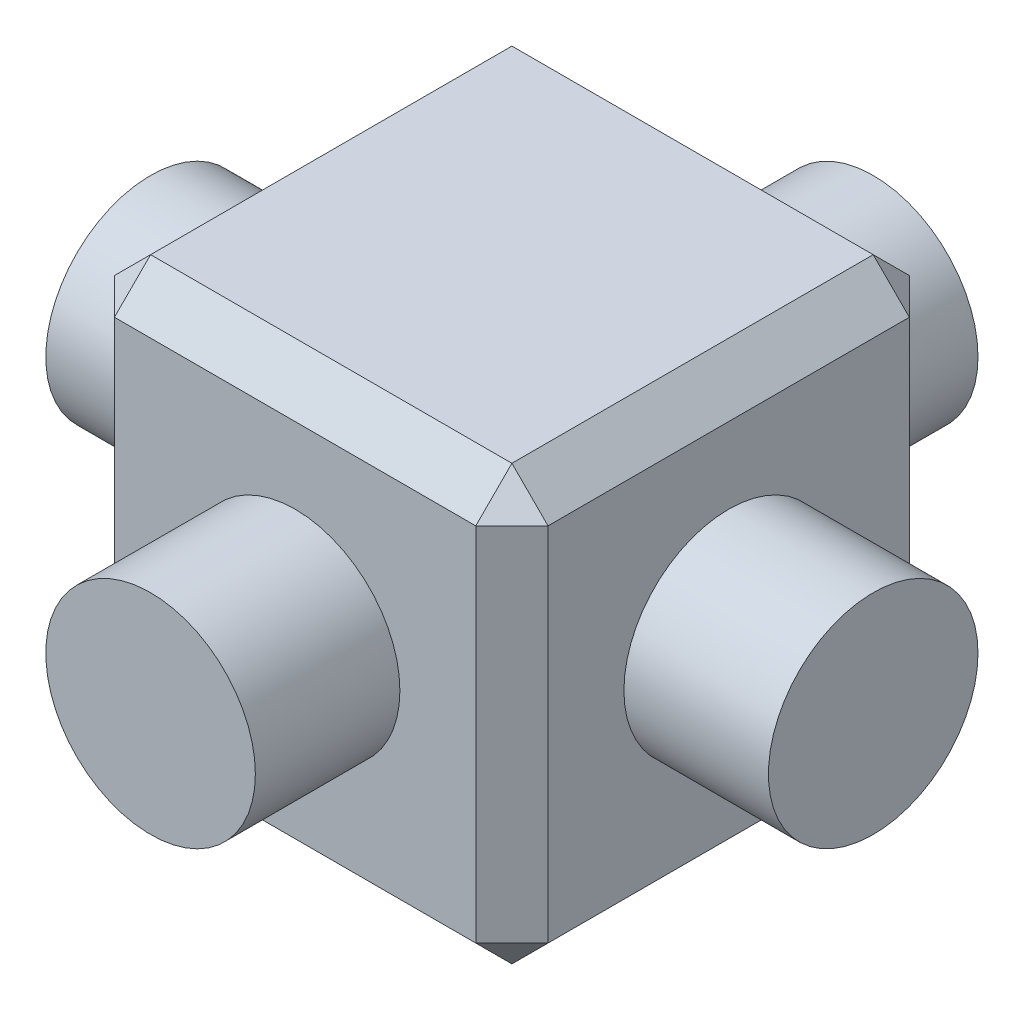
SolidWorks part; units mm, degrees
ref_plane "Front Plane" through (0, 0, 0) normal (0, 0, 1) x (1, 0, 0)
ref_plane "Top Plane" through (0, 0, 0) normal (0, 1, 0) x (1, 0, 0)
ref_plane "Right Plane" through (0, 0, 0) normal (1, 0, 0) x (0, 0, -1)
sketch "Sketch1" plane through (0, 0, 0) normal (0, 1, 0) x (1, 0, 0)
  line L1 (-3, -3) -> (3, -3)
  line L2 (-3, -3) -> (-3, 3)
  line L3 (-3, 3) -> (3, 3)
  line L4 (3, -3) -> (3, 3)
  line L5 (-3, -3) -> (3, 3) construction
  line L6 (-3, 3) -> (3, -3) construction
  point P0 (0, 0)
  dimension "D1" = 6
extrude "Boss-Extrude1" add sketch "Sketch1" along normal blind 6
sketch "Sketch2" plane through (3, 0, 0) normal (1, 0, 0) x (0, 0, -1)
  circle A0 centre (0, 3) radius 1.45
extrude "Boss-Extrude2" add sketch "Sketch2" along normal blind 2 and the other way blind 8
sketch "Sketch3" plane through (0, 0, 3) normal (0, 0, 1) x (1, 0, 0)
  circle A0 centre (0, 3) radius 1.45
extrude "Boss-Extrude3" add sketch "Sketch3" along normal blind 2 and the other way blind 8
chamfer "Chamfer1" distance 0.5 angle 45 12 edges at (0, 0, -3) (3, 0, 0) (3, 3, -3) (0, 0, 3) (3, 3, 3) (-3, 0, 0) (-3, 3, -3) (-3, 3, 3) (3, 6, 0) (0, 6, -3) (0, 6, 3) (-3, 6, 0)
